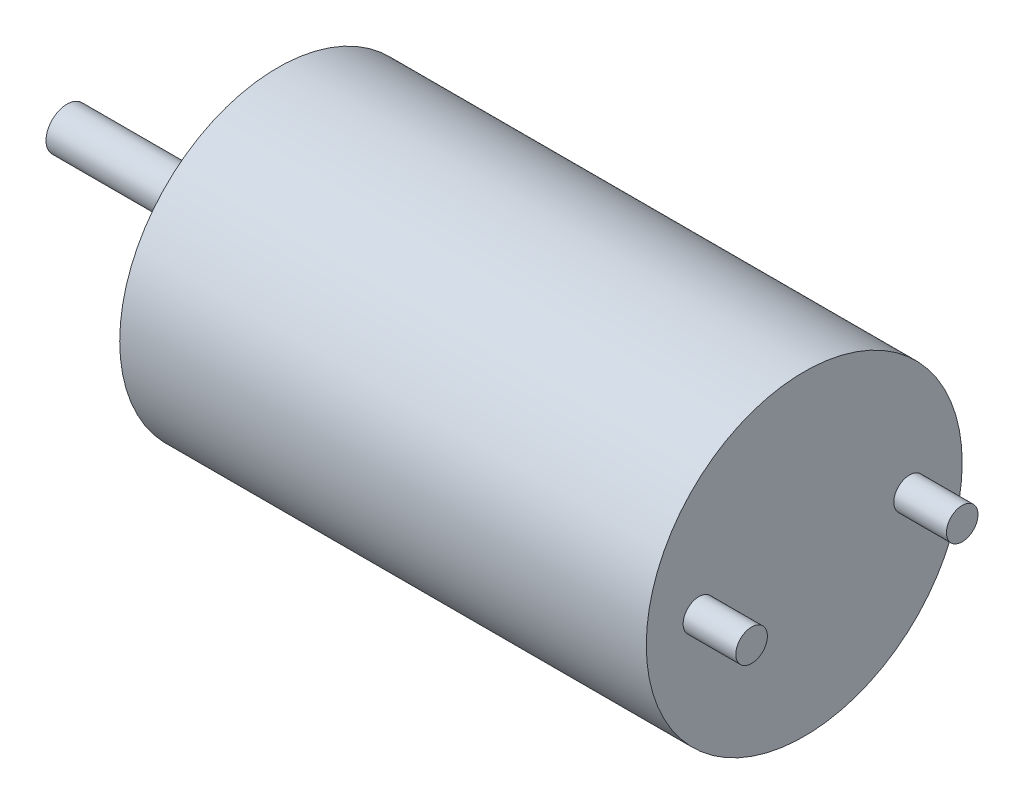
SolidWorks part; units mm, degrees
ref_plane "Front Plane" through (0, 0, 0) normal (0, 0, 1) x (1, 0, 0)
ref_plane "Top Plane" through (0, 0, 0) normal (0, 1, 0) x (1, 0, 0)
ref_plane "Right Plane" through (0, 0, 0) normal (1, 0, 0) x (0, 0, -1)
sketch "Sketch1" plane through (0, 0, 0) normal (1, 0, 0) x (0, 0, -1)
  circle A0 centre (0, 0) radius 3
  dimension "D1" = 6
extrude "Boss-Extrude1" add sketch "Sketch1" along normal blind 10
sketch "Sketch2" plane through (0, 0, 0) normal (-1, 0, 0) x (0, 0, 1)
  circle A0 centre (0, 0) radius 1.2
  dimension "D1" = 2.4
extrude "Boss-Extrude2" add sketch "Sketch2" along normal blind 0.8
sketch "Sketch3" plane through (-0.8, 0, 0) normal (-1, 0, 0) x (0, 0, 1)
  circle A0 centre (0, 0) radius 0.4
  dimension "D1" = 0.8
extrude "Boss-Extrude3" add sketch "Sketch3" along normal blind 3.2
sketch "Sketch4" plane through (10, 0, 0) normal (1, 0, 0) x (0, 0, -1)
  line L0 (-2, 0) -> (2, 0) construction
  circle A0 centre (-2, 0) radius 0.3
  circle A1 centre (2, 0) radius 0.3
  point P4 (0, 0)
  dimension "D2" = 0.6
  dimension "D1" = 4
extrude "Boss-Extrude4" add sketch "Sketch4" along normal blind 1
